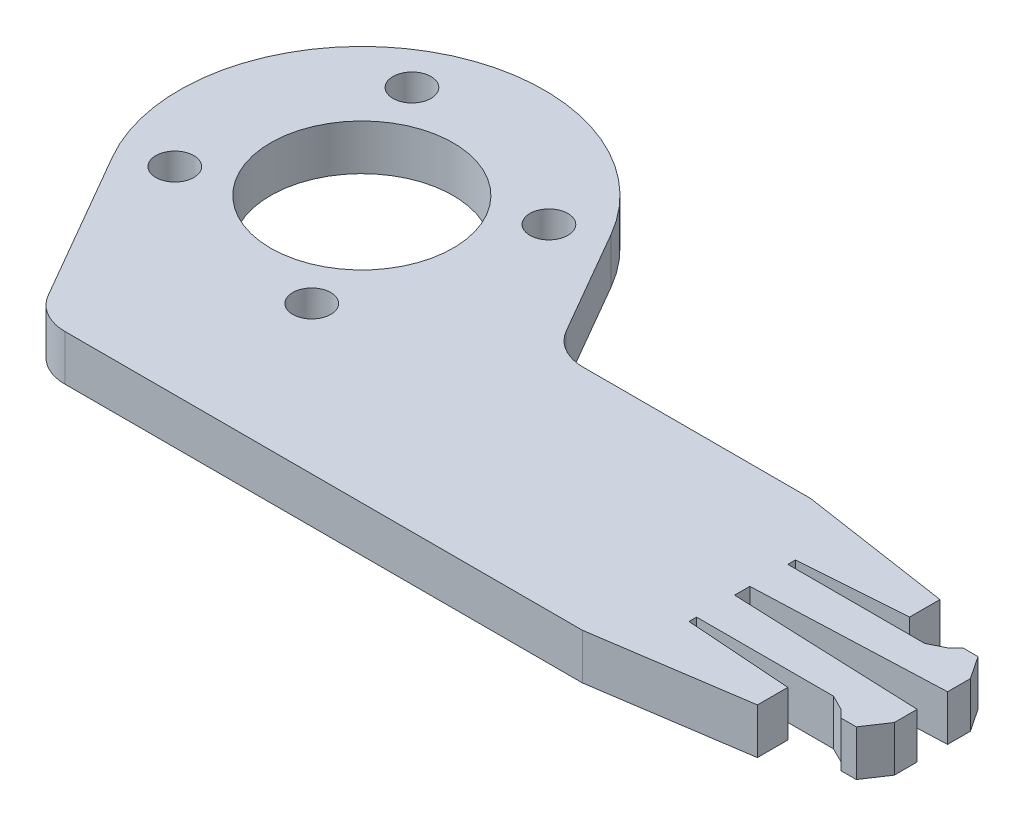
SolidWorks part; units mm, degrees
material "Lasercut ABS"
ref_plane "Front Plane" through (0, 0, 0) normal (0, 0, 1) x (1, 0, 0)
ref_plane "Top Plane" through (0, 0, 0) normal (0, 1, 0) x (1, 0, 0)
ref_plane "Right Plane" through (0, 0, 0) normal (1, 0, 0) x (0, 0, -1)
sketch "Sketch1" plane through (0, 0, 0) normal (0, 1, 0) x (1, 0, 0)
  line L0 (0, 0) -> (0, -10) construction
  line L1 (-4.5, 7.7942) -> (4.5, -7.7942) construction
  line L2 (-7.7942, -4.5) -> (7.7942, 4.5) construction
  line L3 (10.3923, 6) -> (15.2998, -2.5)
  line L4 (15.2998, -2.5) -> (32, -2.5)
  line L5 (-10.3923, -6) -> (-3.7528, -17.5)
  line L6 (-3.7528, -17.5) -> (32, -17.5)
  circle A0 centre (0, 0) radius 6
  circle A1 centre (0, 0) radius 9 construction
  circle A2 centre (7.7942, 4.5) radius 1.25
  circle A3 centre (-4.5, 7.7942) radius 1.25
  circle A4 centre (-7.7942, -4.5) radius 1.25
  circle A5 centre (4.5, -7.7942) radius 1.25
  arc A6 (10.3923, 6) -> (-10.3923, -6) centre (0, 0) ccw
  line B0 (32, -10) -> (35, -10) construction
  line B1 (35, -9.5) -> (35, -10.5)
  line B2 (35, -9.5) -> (47.5, -9)
  line B3 (47.5, -9) -> (47.5, -7.5)
  line B4 (47.5, -7.5) -> (46.5, -6)
  line B5 (46.5, -6) -> (45.5, -6)
  line B6 (45.5, -6) -> (45, -6.5)
  line B7 (45, -6.5) -> (44, -7)
  line B8 (44, -7) -> (35, -7)
  line B9 (35, -7) -> (35, -6.5)
  line B10 (35, -6.5) -> (42, -6)
  line B11 (42, -6) -> (42, -4)
  line B12 (42, -4) -> (32, -2.5)
  line B13 (35, -10.5) -> (47.5, -11)
  line B14 (47.5, -11) -> (47.5, -12.5)
  line B15 (47.5, -12.5) -> (46.5, -14)
  line B16 (46.5, -14) -> (45.5, -14)
  line B17 (45.5, -14) -> (45, -13.5)
  line B18 (45, -13.5) -> (44, -13)
  line B19 (44, -13) -> (35, -13)
  line B20 (35, -13) -> (35, -13.5)
  line B21 (35, -13.5) -> (42, -14)
  line B22 (42, -14) -> (42, -16)
  line B23 (42, -16) -> (32, -17.5)
  dimension "D1" = 12
  dimension "D5" = 18
  dimension "D6" = 2.5
  dimension "D7" = 24
  dimension "D2" = 10
  dimension "D3" = 42
  dimension "D4" = 30
sketch_block_instance "Block-Snap-Textile-1"
sketch_block "Block-Snap-Textile" parameters "D1"=3, "D2"=1, "D3"=2, "D4"=1.5, "D5"=10, "D6"=0.5, "D7"=9, "D8"=1, "D9"=0.5, "D10"=0.5, "D11"=0.5, "D12"=1, "D13"=12.5, "D14"=0.5, "D15"=0.5, "D16"=1.5, "D17"=1.5
extrude "Boss-Extrude1" add sketch "Sketch1" along normal mid plane 3 contours B23 B22 B21 B20 B19 B18 B17 B16 B15 B14 B13 B1 B2 B3 B4 B5 B6 B7 B8 B9 B10 B11 B12 L4 L3 A6 L5 L6 A5 A4 A3 A2 A0
fillet "Fillet1" radius 3 2 edges at (15.2998, 0, 2.5) (-3.7528, 0, 17.5)
sketch "Sketch2" plane through (0, -1.5, 0) normal (0, -1, 0) x (1, 0, 0)
  line L0 (28, 9) -> (12, 9) construction
  line L1 (28, 12.5) -> (12, 12.5) construction
  text T0 "M9" font "1CamBam_Stick_3" height 2.5
  text T1 "ONO V2" font "1CamBam_Stick_3" height 2.5
  dimension "D1" = 3.5
  dimension "D2" = 16
  dimension "D3" = 12
  dimension "D4" = 9
